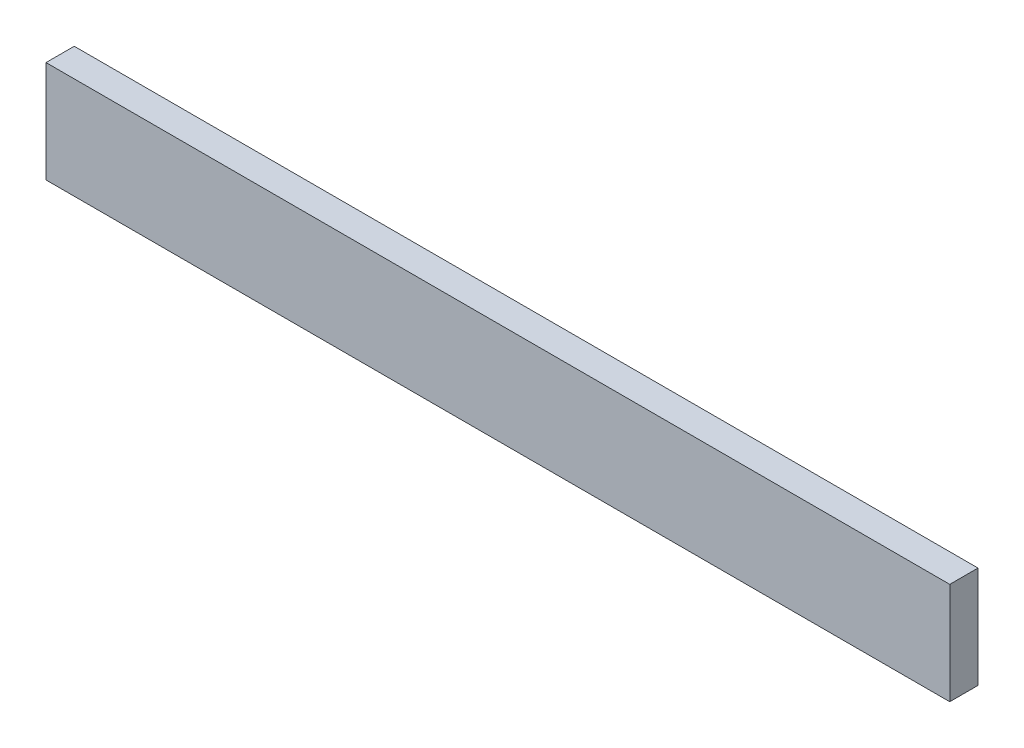
SolidWorks part; units mm, degrees
ref_plane "Front Plane" through (0, 0, 0) normal (0, 0, 1) x (1, 0, 0)
ref_plane "Top Plane" through (0, 0, 0) normal (0, 1, 0) x (1, 0, 0)
ref_plane "Right Plane" through (0, 0, 0) normal (1, 0, 0) x (0, 0, -1)
sketch "Sketch1" plane through (0, 0, 0) normal (0, 0, 1) x (1, 0, 0)
  line L1 (0, 0) -> (800, 0)
  line L2 (0, 0) -> (0, 90)
  line L3 (0, 90) -> (800, 90)
  line L4 (800, 0) -> (800, 90)
  point P5 (959.5489, 90)
  dimension "D1" = 90
  dimension "D2" = 800
extrude "Boss-Extrude1" add sketch "Sketch1" along normal blind 25
